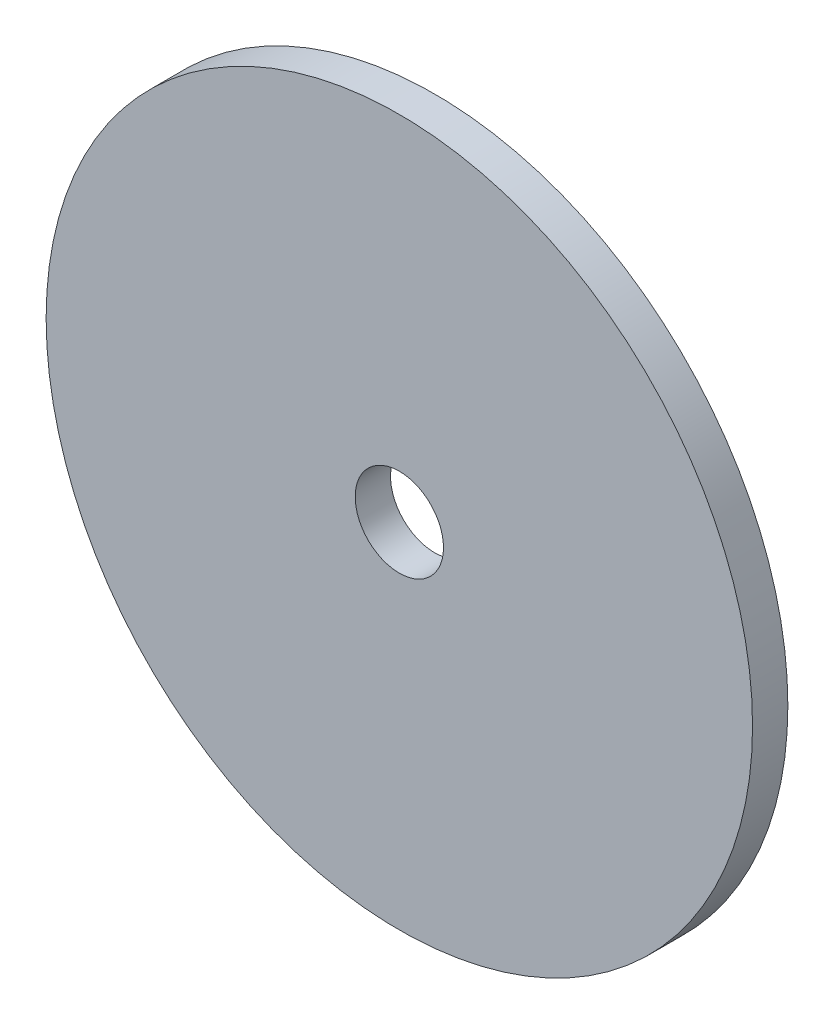
SolidWorks part; units mm, degrees
ref_plane "Front Plane" through (0, 0, 0) normal (0, 0, 1) x (1, 0, 0)
ref_plane "Top Plane" through (0, 0, 0) normal (0, 1, 0) x (1, 0, 0)
ref_plane "Right Plane" through (0, 0, 0) normal (1, 0, 0) x (0, 0, -1)
sketch "Sketch1" plane through (0, 0, 0) normal (0, 0, 1) x (1, 0, 0)
  circle A0 centre (0, 0) radius 25.4
  circle A1 centre (0, 0) radius 3.175
  dimension "D1" = 6.35
  dimension "D2" = 50.8
extrude "Boss-Extrude1" add sketch "Sketch1" along normal blind 2.54
